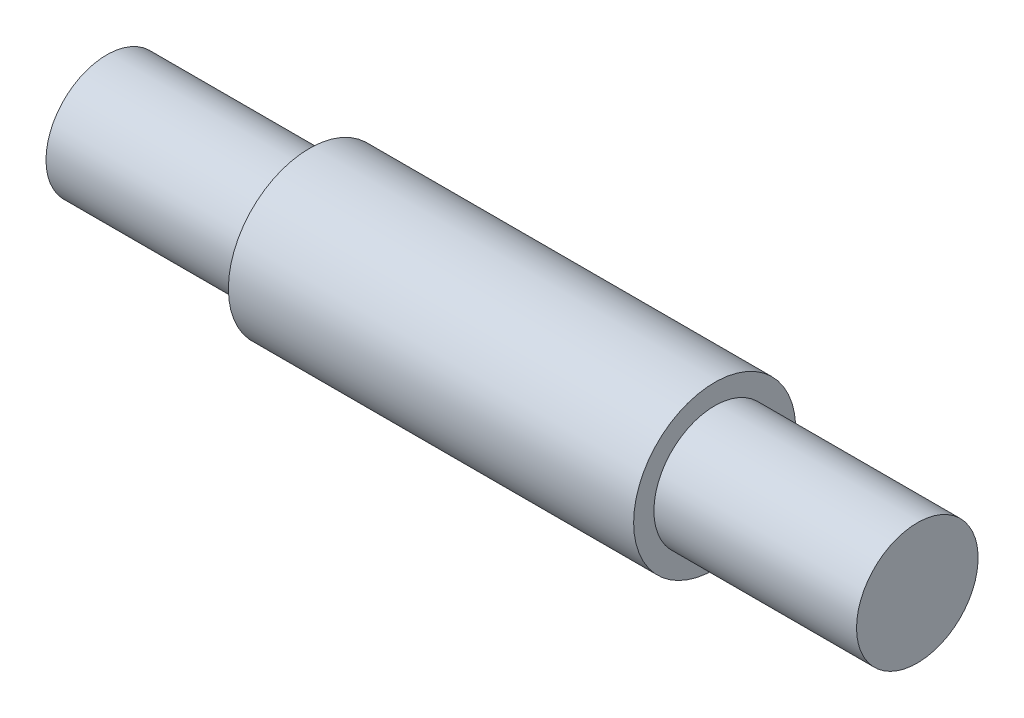
SolidWorks part; units mm, degrees
ref_plane "Front Plane" through (0, 0, 0) normal (0, 0, 1) x (1, 0, 0)
ref_plane "Top Plane" through (0, 0, 0) normal (0, 1, 0) x (1, 0, 0)
ref_plane "Right Plane" through (0, 0, 0) normal (1, 0, 0) x (0, 0, -1)
other "Configuration Table"
sketch "Sketch1" plane through (0, 0, 0) normal (0, 0, 1) x (1, 0, 0)
  line L0 (-50, 0) -> (50, 0) construction
  line L1 (-40, 0) -> (40, 0)
  line L2 (40, 0) -> (40, 6)
  line L3 (40, 6) -> (20, 6)
  line L4 (20, 6) -> (20, 8)
  line L5 (20, 8) -> (-20, 8)
  line L6 (0, 30) -> (0, -20) construction
  line L7 (-20, 6) -> (-20, 8)
  line L8 (-40, 6) -> (-20, 6)
  line L9 (-40, 0) -> (-40, 6)
  point P12 (0, 8)
  point P15 (0, 0)
  dimension "D1" = 12
  dimension "D2" = 16
  dimension "D3" = 40
  dimension "D4" = 20
revolve "Revolve1" add sketch "Sketch1" angle 360 about L0
